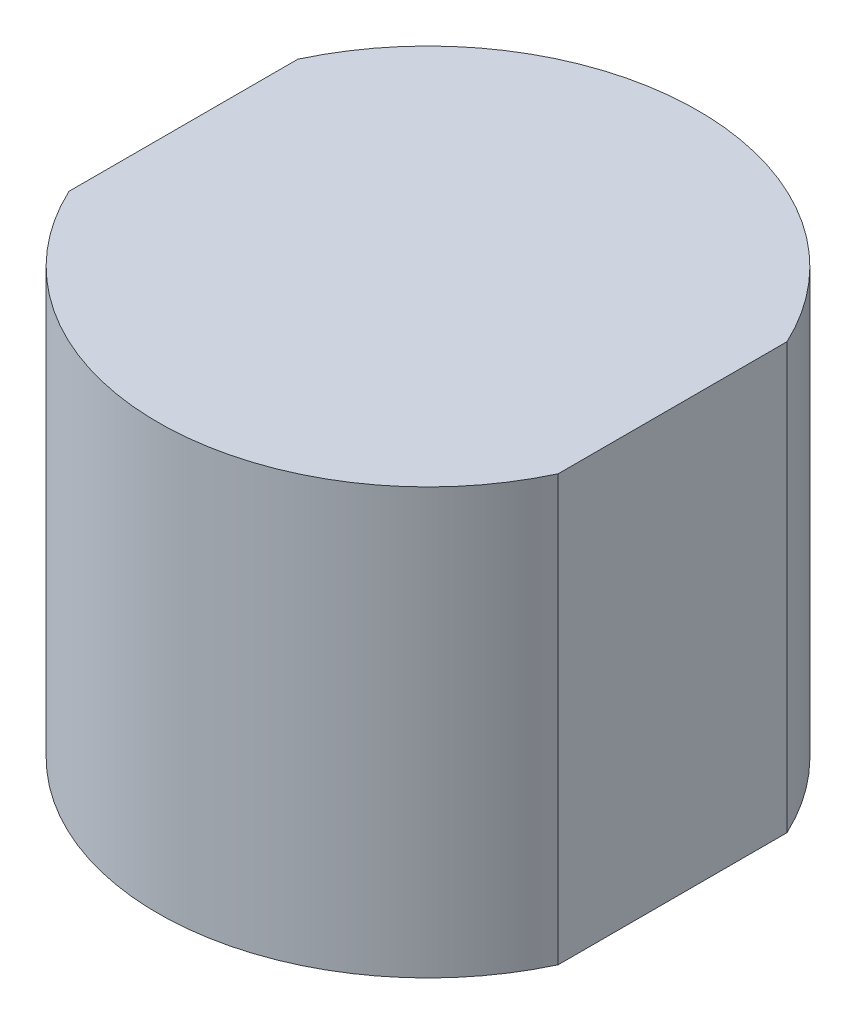
SolidWorks part; units mm, degrees
ref_plane "Front Plane" through (0, 0, 0) normal (0, 0, 1) x (1, 0, 0)
ref_plane "Top Plane" through (0, 0, 0) normal (0, 1, 0) x (1, 0, 0)
ref_plane "Right Plane" through (0, 0, 0) normal (1, 0, 0) x (0, 0, -1)
sketch "Sketch1" plane through (0, 0, 0) normal (0, 1, 0) x (1, 0, 0)
  line L0 (5.7521, -2.69) -> (5.7521, 2.69)
  line L1 (-5.7521, -2.69) -> (-5.7521, 2.69)
  circle A1 centre (0, 0) radius 6.35
extrude "Boss-Extrude1" add sketch "Sketch1" along normal blind 10 contours L0 A1 L1
